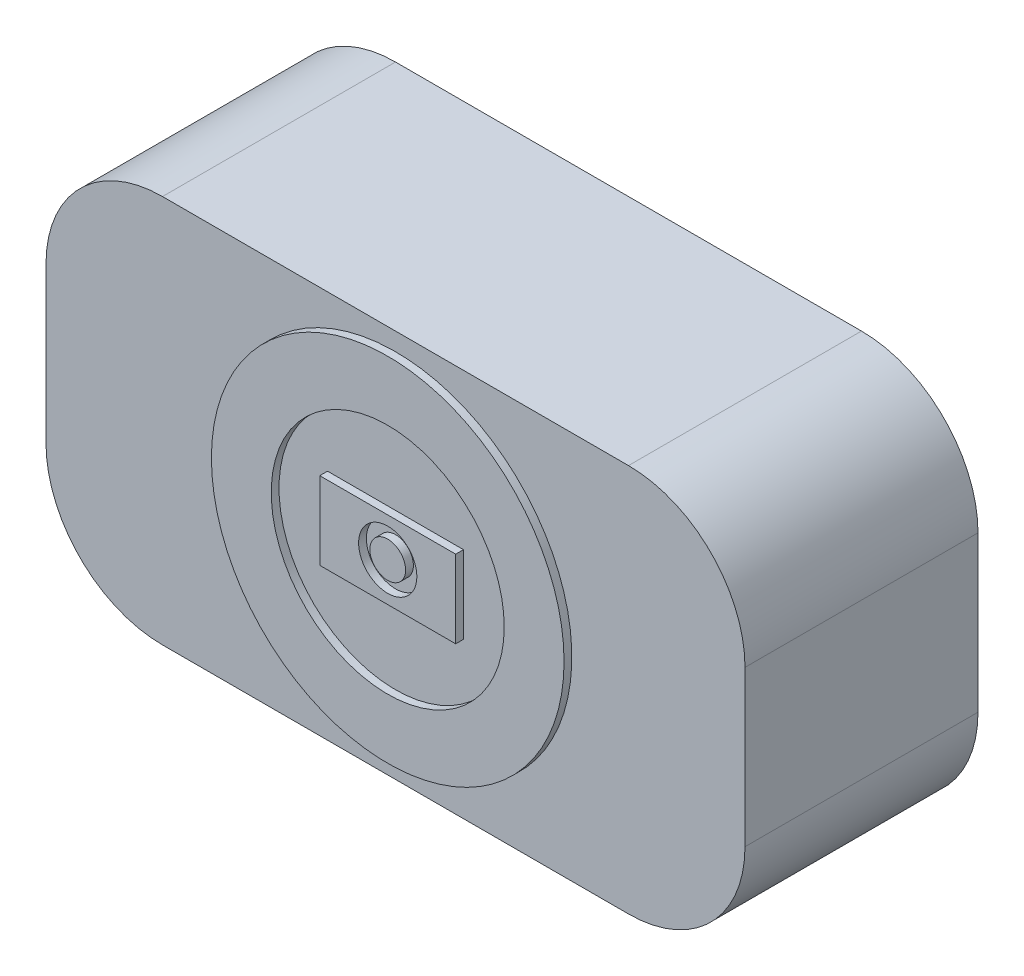
SolidWorks part; units mm, degrees
ref_plane "Front Plane" through (0, 0, 0) normal (0, 0, 1) x (1, 0, 0)
ref_plane "Top Plane" through (0, 0, 0) normal (0, 1, 0) x (1, 0, 0)
ref_plane "Right Plane" through (0, 0, 0) normal (1, 0, 0) x (0, 0, -1)
sketch "Sketch1" plane through (0, 0, 0) normal (0, 0, 1) x (1, 0, 0)
  line L1 (0, 0) -> (90, 0)
  line L2 (0, 0) -> (0, 50)
  line L3 (0, 50) -> (90, 50)
  line L4 (90, 0) -> (90, 50)
  dimension "D1" = 90
  dimension "D2" = 50
extrude "Boss-Extrude1" add sketch "Sketch1" against normal blind 30
fillet "Fillet1" radius 15 4 edges at (90, 0, -15) (0, 0, -15) (0, 50, -15) (90, 50, -15)
sketch "Sketch2" plane through (0, 0, 0) normal (0, 0, 1) x (1, 0, 0)
  circle A4 centre (45, 25) radius 22.7034
extrude "Boss-Extrude2" add sketch "Sketch2" along normal blind 1
sketch "Sketch3" plane through (0, 0, 1) normal (0, 0, 1) x (1, 0, 0)
  circle A0 centre (45, 25) radius 15
  dimension "D1" = 30
extrude "Cut-Extrude1" cut sketch "Sketch3" against normal blind 1
sketch "Sketch4" plane through (0, 0, 0) normal (0, 0, 1) x (1, 0, 0)
  line L0 (75, 50) -> (15, 50) construction
  line L1 (36.25, 20) -> (53.75, 20)
  line L2 (36.25, 20) -> (36.25, 30)
  line L3 (36.25, 30) -> (53.75, 30)
  line L4 (53.75, 20) -> (53.75, 30)
  line L5 (90, 15) -> (90, 35) construction
  dimension "D1" = 17.5
  dimension "D2" = 10
  dimension "D3" = 20
  dimension "D4" = 36.25
extrude "Boss-Extrude3" add sketch "Sketch4" along normal blind 1
sketch "Sketch5" plane through (0, 0, 1) normal (0, 0, 1) x (1, 0, 0)
  circle A0 centre (45, 25) radius 3.75
  dimension "D1" = 7.5
extrude "Cut-Extrude2" cut sketch "Sketch5" against normal blind 1
sketch "Sketch6" plane through (0, 0, 0) normal (0, 0, 1) x (1, 0, 0)
  circle A0 centre (45, 25) radius 2.3033
extrude "Boss-Extrude4" add sketch "Sketch6" along normal blind 1
